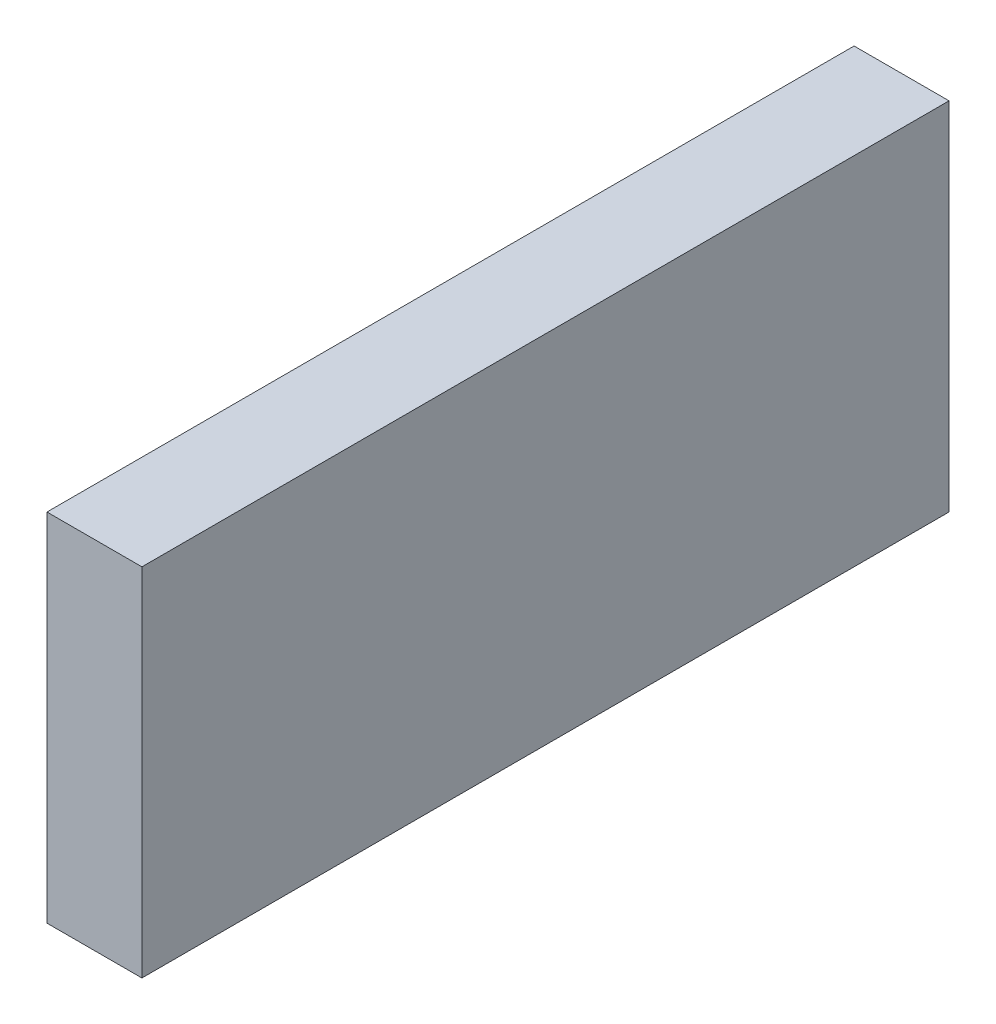
SolidWorks part; units mm, degrees
ref_plane "Front Plane" through (0, 0, 0) normal (0, 0, 1) x (1, 0, 0)
ref_plane "Top Plane" through (0, 0, 0) normal (0, 1, 0) x (1, 0, 0)
ref_plane "Right Plane" through (0, 0, 0) normal (1, 0, 0) x (0, 0, -1)
sketch "Sketch1" plane through (0, 0, 0) normal (0, 1, 0) x (1, 0, 0)
  line L1 (20, 170) -> (-20, 170)
  line L2 (20, 170) -> (20, -170)
  line L3 (20, -170) -> (-20, -170)
  line L4 (-20, 170) -> (-20, -170)
  line L5 (20, 170) -> (-20, -170) construction
  line L6 (20, -170) -> (-20, 170) construction
  point P0 (0, 0)
  dimension "D1" = 340
  dimension "D2" = 40
extrude "Boss-Extrude1" add sketch "Sketch1" along normal blind 150
